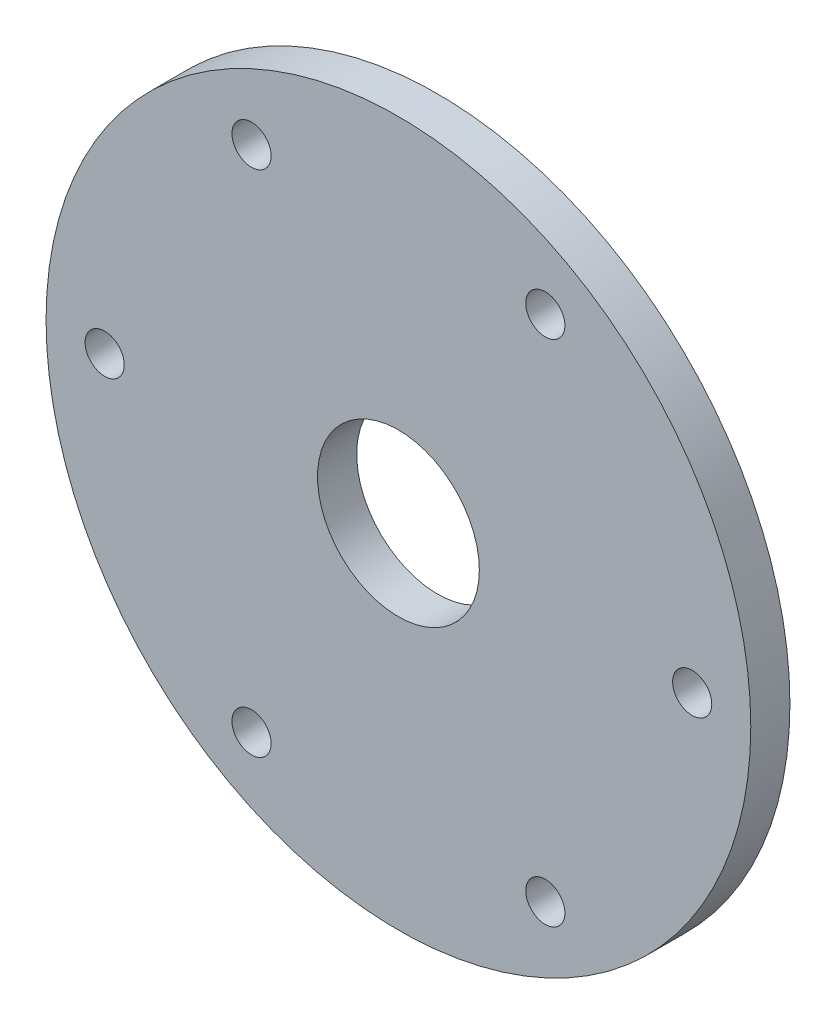
SolidWorks part; units mm, degrees
ref_plane "前视基准面" through (0, 0, 0) normal (0, 0, 1) x (1, 0, 0)
ref_plane "上视基准面" through (0, 0, 0) normal (0, 1, 0) x (1, 0, 0)
ref_plane "右视基准面" through (0, 0, 0) normal (1, 0, 0) x (0, 0, -1)
sketch "草图2" plane through (0, 0, 0) normal (0, 0, 1) x (1, 0, 0)
  circle A0 centre (0, 0) radius 27
  circle A1 centre (0, 0) radius 6.2
  circle A2 centre (22.51, 0) radius 1.5
  circle A3 centre (11.255, -19.4942) radius 1.5
  circle A4 centre (-11.255, -19.4942) radius 1.5
  circle A5 centre (-22.51, 0) radius 1.5
  circle A6 centre (-11.255, 19.4942) radius 1.5
  circle A7 centre (11.255, 19.4942) radius 1.5
  point P18 (0, 0)
  dimension "D1" = 6
extrude "凸台-拉伸1" add sketch "草图2" along normal blind 3
